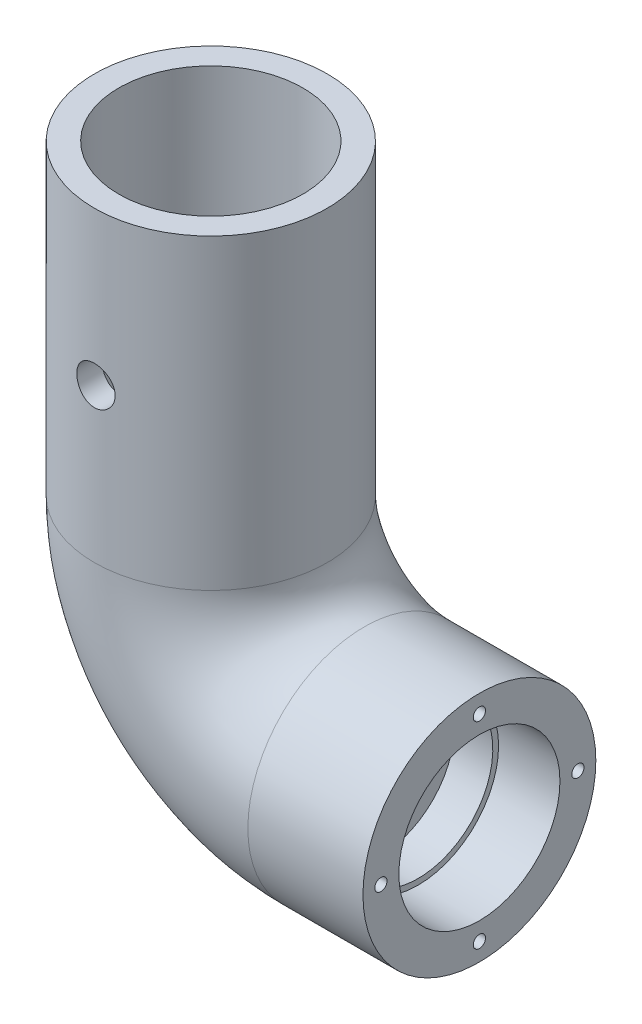
SolidWorks part; units mm, degrees
material "Hexcel AS4C (3000 Filaments)"
ref_plane "Front Plane" through (0, 0, 0) normal (0, 0, 1) x (1, 0, 0)
ref_plane "Top Plane" through (0, 0, 0) normal (0, 1, 0) x (1, 0, 0)
ref_plane "Right Plane" through (0, 0, 0) normal (1, 0, 0) x (0, 0, -1)
sketch "Sketch1" plane through (0, 0, 0) normal (0, 1, 0) x (1, 0, 0)
  line L0 (0, 12) -> (0, 15.175) construction
  circle A0 centre (0, 0) radius 15.175
  circle A1 centre (0, 0) radius 12
  dimension "D1" = 24
  dimension "D2" = 3.175
sketch "Sketch2" plane through (0, 0, 0) normal (0, 0, 1) x (1, 0, 0)
  line L0 (0, 0) -> (0, -40)
  line L1 (20, -60) -> (35, -60)
  arc A0 (0, -40) -> (20, -60) centre (20, -40) ccw
  point P6 (0, -60)
  dimension "D3" = 20
  dimension "D1" = 60
  dimension "D2" = 35
sweep "Sweep1" add profiles "Sketch1" path "Sketch2"
ref_plane "Plane4" through (20, 0, 0) normal (1, 0, 0) x (0, 0, -1)
sketch "Sketch3" plane through (20, 0, 0) normal (1, 0, 0) x (0, 0, -1)
  circle A0 centre (0, -60) radius 12
  circle A1 centre (0, -60) radius 12 construction
extrude "Boss-Extrude1" add sketch "Sketch3" along normal blind 2
sketch "Sketch4" plane through (22, 0, 0) normal (1, 0, 0) x (0, 0, -1)
  circle A0 centre (0, -60) radius 9.75
  circle A1 centre (0, -60) radius 12
  circle A2 centre (0, -60) radius 12 construction
  dimension "D1" = 19.5
extrude "Boss-Extrude4" add sketch "Sketch4" along normal blind 5
sketch "Sketch6" plane through (27, 0, 0) normal (1, 0, 0) x (0, 0, -1)
  circle A0 centre (0, -60) radius 12
  circle A1 centre (0, -60) radius 10.5
  circle A2 centre (0, -60) radius 12 construction
  dimension "D1" = 21
extrude "Boss-Extrude5" add sketch "Sketch6" along normal up to surface (8 mm away) up to face at (35, -60, 12)
sketch "Sketch7" plane through (0, 0, 0) normal (0, 0, 1) x (1, 0, 0)
  circle A0 centre (0, -20) radius 2.5
  circle A1 centre (0, -20) radius 2.5 construction
  dimension "D1" = 20
extrude "Cut-Extrude2" cut sketch "Sketch7" against normal through all both and the other way through all
sketch "Sketch8" plane through (35, 0, 0) normal (1, 0, 0) x (0, 0, -1)
  line L0 (0, -47.1625) -> (0, -44.825) construction
  line L1 (0, -47.1625) -> (0, -49.5) construction
  circle A0 centre (0, -60) radius 12.8375 construction
  circle A1 centre (0, -60) radius 15.175 construction
  circle A2 centre (0, -60) radius 10.5 construction
  point P4 (-12.8375, -60)
  point P12 (12.8375, -60)
  point P13 (0, -72.8375)
hole_wizard "Tap Drill for M2x0.4 Tap1" positions "Sketch9" profile "Sketch10" hole size "M2x0.4" standard "ANSI Metric"
sketch "Sketch9" plane through (35, 0, 0) normal (1, 0, 0) x (0, 0, -1)
  point P0 (0, -47.1625)
  point P3 (12.8375, -60)
  point P6 (0, -72.8375)
  point P9 (-12.8375, -60)
sketch "Sketch10" plane through (35, -47.1625, 0) normal (0, 1, 0) x (0, 0, -1)
  line L0 (0, 0) -> (0, 10.4807)
  line L1 (0, 10.4807) -> (0.8, 10)
  line L2 (0.8, 10) -> (0.8, 0)
  line L5 (0.8, 0) -> (0, 0)
  line L10 (0, 10.4807) -> (-0.8, 10) construction
  line L11 (0, -6.35) -> (0, 107.95) construction
  dimension "Hole Dia." = 1.6
  dimension "Hole Depth" = 10
  dimension "Drill Angle" = 118
equation "\"tubeOutDiameter\" = 35mm"
equation "\"wheelShaftDiameter\"= 12mm"
equation "\"wheelThickness\"= 135mm"
equation "\"BearingDiameter\"= 20mm"
equation "\"BearingThickness\"= 10mm"
equation "\"frontShaftDiameter\"= 20mm"
equation "\"D1@Sketch1\"=\"wheelShaftDiameter\"*2"
